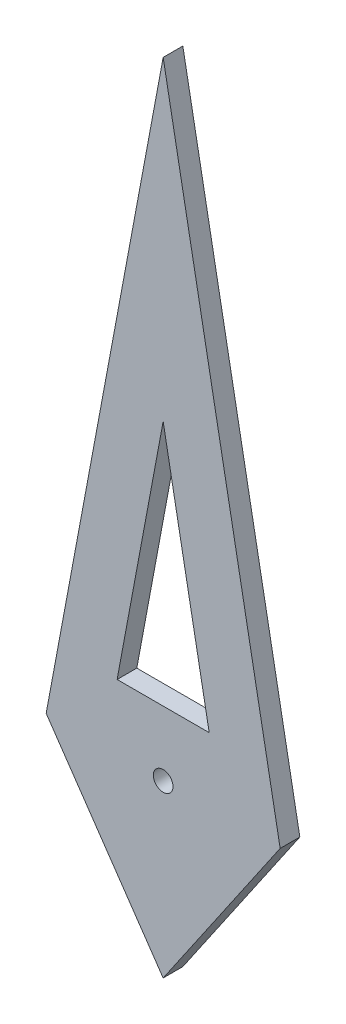
SolidWorks part; units mm, degrees
ref_plane "Front Plane" through (0, 0, 0) normal (0, 0, 1) x (1, 0, 0)
ref_plane "Top Plane" through (0, 0, 0) normal (0, 1, 0) x (1, 0, 0)
ref_plane "Right Plane" through (0, 0, 0) normal (1, 0, 0) x (0, 0, -1)
sketch "Sketch1" plane through (0, 0, 0) normal (0, 0, 1) x (1, 0, 0)
  line L0 (0, 0) -> (0, 3.5259) construction
  line L1 (0, 3.184) -> (0.5945, 0)
  line L2 (0.5945, 0) -> (0, -0.8676)
  line L3 (-0.5945, 0) -> (0, -0.8676)
  line L4 (0, 3.184) -> (-0.5945, 0)
  line L5 (-0.234, 0.3292) -> (0.234, 0.3292)
  line L6 (0.234, 0.3292) -> (0, 1.5821)
  line L7 (-0.234, 0.3292) -> (0, 1.5821)
  circle A0 centre (0, 0) radius 0.05
  point P11 (0, 0.3292)
extrude "Boss-Extrude1" add sketch "Sketch1" along normal blind 0.1
